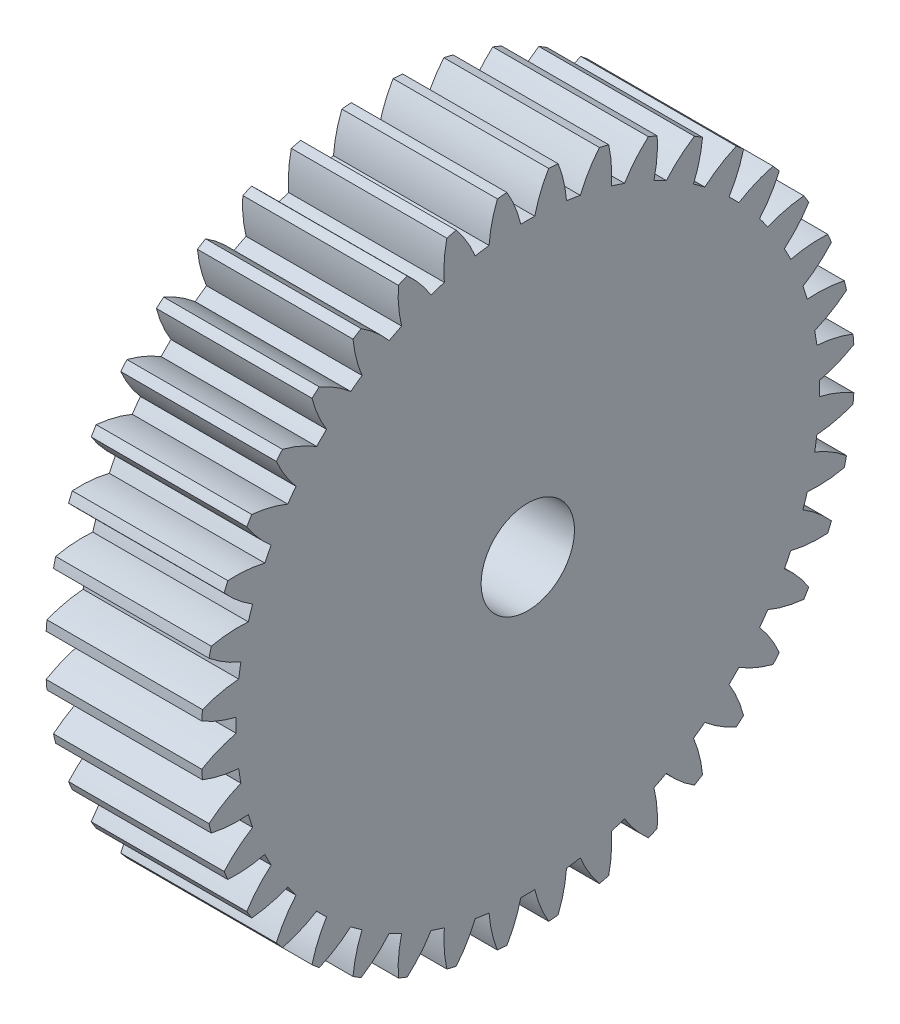
SolidWorks part; units mm, degrees
material "1.0035 (S185)"
ref_plane "Plane1" through (0, 0, 0) normal (0, 0, 1) x (1, 0, 0)
ref_plane "Plane2" through (0, 0, 0) normal (0, 1, 0) x (1, 0, 0)
ref_plane "Plane3" through (0, 0, 0) normal (1, 0, 0) x (0, 0, -1)
sketch "HoldingSke" plane through (0, 0, 0) normal (0, 1, 0) x (1, 0, 0)
  line L0 (0, 0) -> (1.5321, -1.2856)
  line L1 (-15, 0) -> (100, 0) construction
  line L2 (0, 0) -> (-2.1039, 2.3779)
  line L3 (0, 0) -> (-11.863, 4.5341)
  line L4 (0, 0) -> (6.6156, 5.5511)
  line L5 (0, 0) -> (-46.8476, -17.4728)
  line L6 (0, 0) -> (-4.1448, -2.7965)
  line L7 (-2.1039, 2.3779) -> (8.6586, 51.2059)
  line L8 (-76.2, 54.61) -> (-75.7, 54.61)
  line L9 (-71.009, 38.7566) -> (-53.1078, 45.2721)
  line L10 (-76.2, 71.12) -> (104.1128, 71.12)
  line L11 (0, 0) -> (-5, 0)
  line L12 (-76.2, 101.6) -> (-76.181, 101.6)
  line L13 (24.9733, 27.94) -> (52.9518, 28.4284)
  line L14 (24.9733, 27.94) -> (24.9743, 27.94)
  line L15 (24.9733, 27.94) -> (100.4006, 29.5858)
  line L16 (-63.627, -0.5) -> (-12.827, -0.5)
  circle A0 centre (0, 0) radius 1.5
  circle A1 centre (0, 0) radius 9.374
  circle A2 centre (0, 0) radius 37.5
  circle A3 centre (0, 0) radius 1.5
  dimension "MHD" = 18.748
  dimension "Hub_dia" = 75
  dimension "Bore" = 3
  dimension "MBD" = 3
  dimension "Num_teeth" = 40
  dimension "Pitch_radius" = 180.3128
  dimension "Pitch" = 2
  dimension "Width" = 5
  dimension "Overall_len" = 50
  dimension "Show_teeth" = 40
  dimension "Thickness" = 5
  dimension "OAL" = 50.0001
  dimension "T_dim" = 0.5
  dimension "Ap" = 20
  dimension "H" = 19.05
  dimension "Backlash" = 0.019
  dimension "Addendum_fac" = 1
  dimension "Dedendum_fac" = 1.25
  dimension "Clearance_fac" = 0.25
  dimension "Dedendum_add" = 0.001
  dimension "Module" = 0.5
sketch "BasProSke" plane through (0, 0, 0) normal (0, 1, 0) x (1, 0, 0)
  line L0 (-10, 0) -> (60, 0) construction
  line L1 (0, 0) -> (0, 10.5)
  line L2 (0, 0) -> (5, 0)
  line L3 (5, 0) -> (5, 10.5)
  line L4 (5, 10.5) -> (0, 10.5)
  dimension "Diameter" = 21
  dimension "Thickness" = 5
revolve "Base-Revolve" add sketch "BasProSke" angle 360 about L0
sketch "TooCutSke" plane through (0, 0, 0) normal (1, 0, 0) x (0, 0, -1)
  line L1 (0, 0) -> (0, 107) construction
  line L2 (0, 0) -> (-0.4258, 9.9909) construction
  line L3 (0, 0) -> (-1.5682, 19.9255) construction
  line L4 (-0.4258, 9.9909) -> (-0.7841, 9.9627) construction
  arc A0 (0.2242, 9.3713) -> (-0.2242, 9.3713) centre (0, 0) ccw
  arc A1 (0.6847, 10.5031) -> (-0.6847, 10.5031) centre (0, 0) ccw
  circle A2 centre (0, 0) radius 10 construction
  circle A3 centre (0, 0) radius 9.3969 construction
  arc A4 (-0.2242, 9.3713) -> (-0.6847, 10.5031) centre (-4.1161, 8.4475) ccw
  arc A5 (0.6847, 10.5031) -> (0.2242, 9.3713) centre (4.1161, 8.4475) ccw
  dimension "Root_dia" = 18.748
  dimension "Overcut_dia" = 21.0508
  dimension "Pitch_dia" = 20
  dimension "Base_dia" = 18.7939
  dimension "Flank_rad" = 4
  dimension "Half_ang" = 4.5
  dimension "Half_CT" = 0.3593
extrude "ToothCut" cut sketch "TooCutSke" along normal through all
fillet "Breaks" [suppressed] radius 0.01
fillet "RootFillets" [suppressed] radius 0.126
pattern_circular "TeethCuts" count 40 every 9 about axis through (-10, 0, 0) along (1, 0, 0) of "ToothCut", "RootFillets", "Breaks"
sketch "HubNeaOneSke" plane through (0, 0, 0) normal (-1, 0, 0) x (0, 0, 1)
  circle A0 centre (0, 0) radius 9.374
  dimension "Diameter" = 18.748
extrude "HubNearOne" [suppressed] add sketch "HubNeaOneSke" along normal blind 45.0001
sketch "HubNeaBotSke" plane through (0, 0, 0) normal (-1, 0, 0) x (0, 0, 1)
  circle A0 centre (0, 0) radius 9.374
  dimension "Diameter" = 18.748
extrude "HubNearBoth" [suppressed] add sketch "HubNeaBotSke" along normal blind 22.5
ref_plane "FarPln" through (5, 0, 0) normal (1, 0, 0) x (0, 0, -1)
sketch "HubFarSke" plane through (5, 0, 0) normal (1, 0, 0) x (0, 0, -1)
  circle A0 centre (0, 0) radius 9.374
  dimension "Diameter" = 18.748
extrude "HubFar" [suppressed] add sketch "HubFarSke" along normal blind 22.5
sketch "BorSke" plane through (0, 0, 0) normal (1, 0, 0) x (0, 0, -1)
  circle A0 centre (0, 0) radius 1.5
  dimension "Diameter" = 3
extrude "Bore" cut sketch "BorSke" along normal mid plane 100.0001
sketch "KeySke" plane through (0, 0, 0) normal (1, 0, 0) x (0, 0, -1)
  line L0 (-0.6, 0) -> (-0.6, 2)
  line L1 (-0.6, 2) -> (0.6, 2)
  line L2 (0.6, 2) -> (0.6, 0)
  line L3 (0, 0) -> (0, 34) construction
  line L4 (-0.6, 0) -> (0.6, 0)
  dimension "Offset" = 2
  dimension "Width" = 1.2
extrude "Keyway" [suppressed] cut sketch "KeySke" along normal mid plane 100.0001
pattern_circular "Keyway2" [suppressed] count 2 every 90 about axis through (-10, 0, 0) along (1, 0, 0)
equation "' \"Module@HoldingSke\" = 6.35"
equation "' \"Num_teeth@HoldingSke\" = 12"
equation "' \"Ap@HoldingSke\" =  20"
equation "' \"Width@HoldingSke\" = 0.5 * 25.4"
equation "' \"Hub_dia@HoldingSke\"= 1 * 25.4"
equation "' \"Overall_len@HoldingSke\" = 1.0 * 25.4"
equation "' \"Bore@HoldingSke\" = 0.75 * 25.4"
equation "' \"T_dim@HoldingSke\" = 0.1 * 25.4"
equation "' \"Width@KeySke\" = 0.25 * 25.4"
equation "' \"Show_teeth@HoldingSke\" = 13"
equation "' \"Backlash@HoldingSke\" = 0.009 * 25.4"
equation "' \"Addendum_fac@HoldingSke\" = 1.0"
equation "' \"Dedendum_fac@HoldingSke\" = 1.25"
equation "' \"Dedendum_add@HoldingSke\" = 0.00005 * 25.4"
equation "' \"Clearance_fac@HoldingSke\" = 0.25"
equation "\"Pitch@HoldingSke\" = 1 / \"Module@HoldingSke\""
equation "\"Overcut_dia@TooCutSke\" = (\"Num_teeth@HoldingSke\" + 2 * \"Addendum_fac@HoldingSke\") / \"Pitch@HoldingSke\" + 0.002 * 25.4"
equation "\"Pitch_dia@TooCutSke\" = \"Num_teeth@HoldingSke\" / \"Pitch@HoldingSke\""
equation "\"Base_dia@TooCutSke\" = \"Num_teeth@HoldingSke\" / \"Pitch@HoldingSke\" * cos((\"Ap@HoldingSke\"  * 3.14159265 / 180))"
equation "\"Root_dia@TooCutSke\" = (\"Num_teeth@HoldingSke\" + 2) / \"Pitch@HoldingSke\" - 2 * (\"Addendum_fac@HoldingSke\" + \"Dedendum_fac@HoldingSke\") / \"Pitch@HoldingSke\" - \"Dedendum_add@HoldingSke\" * 2"
equation "\"Half_ang@TooCutSke\" = 180 / \"Num_teeth@HoldingSke\""
equation "\"Half_CT@TooCutSke\" = \"Num_teeth@HoldingSke\" / \"Pitch@HoldingSke\" * sin((3.14159265 / 2 / \"Num_teeth@HoldingSke\")) / 2 - 7 * \"Backlash@HoldingSke\" / 4"
equation "\"Flank_rad@TooCutSke\" = \"Num_teeth@HoldingSke\" / \"Pitch@HoldingSke\" / 5"
equation "\"Radius@RootFillets\" = \"Clearance_fac@HoldingSke\" / \"Pitch@HoldingSke\" + \"Dedendum_add@HoldingSke\""
equation "\"Break_rad@Breaks\" = 0.02 / \"Pitch@HoldingSke\""
equation "\"Thickness@HoldingSke\" = \"Width@HoldingSke\""
equation "\"OAL@HoldingSke\" = \"Thickness@HoldingSke\""
equation "\"MHD@HoldingSke\" = (\"Num_teeth@HoldingSke\" + 2) / \"Pitch@HoldingSke\" - 2 * (\"Addendum_fac@HoldingSke\" + \"Dedendum_fac@HoldingSke\")  / \"Pitch@HoldingSke\" - \"Dedendum_add@HoldingSke\" * 2"
equation "\"MBD@HoldingSke\" = (\"Num_teeth@HoldingSke\" + 2) / \"Pitch@HoldingSke\" - 2 * (\"Addendum_fac@HoldingSke\" + \"Dedendum_fac@HoldingSke\")  / \"Pitch@HoldingSke\" - \"Dedendum_add@HoldingSke\" * 2 - 0.002 * 25.4"
equation "\"MHD@HoldingSke\" = ((sgn( \"MHD@HoldingSke\" - \"Hub_dia@HoldingSke\" )-1)*( \"MHD@HoldingSke\" - \"Hub_dia@HoldingSke\" ))/-2+ \"Hub_dia@HoldingSke\""
equation "\"MBD@HoldingSke\" = ((sgn( \"MBD@HoldingSke\" - \"Bore@HoldingSke\" )-1)*( \"MBD@HoldingSke\" - \"Bore@HoldingSke\" ))/-2+ \"Bore@HoldingSke\""
equation "\"OAL@HoldingSke\" = ((sgn( \"OAL@HoldingSke\" - \"Overall_len@HoldingSke\" )+1)*( \"OAL@HoldingSke\" - \"Overall_len@HoldingSke\" ))/2 + \"Overall_len@HoldingSke\" + 0.000002 * 25.4"
equation "\"Num_teeth@TeethCuts\" = int( \"Show_teeth@HoldingSke\" ) + 1"
equation "\"Num_teeth@TeethCuts\" = ((sgn( \"Num_teeth@TeethCuts\" - \"Num_teeth@HoldingSke\" )-1)*( \"Num_teeth@TeethCuts\" - \"Num_teeth@HoldingSke\" ))/-2+ \"Num_teeth@HoldingSke\""
equation "\"Num_teeth@TeethCuts\" = ((sgn( \"Num_teeth@TeethCuts\" - 2.0)+1)*( \"Num_teeth@TeethCuts\" - 2.0))/2 +2.0"
equation "\"Angle@TeethCuts\" = 360.0 / \"Num_teeth@HoldingSke\""
equation "\"Diameter@BasProSke\" = (\"Num_teeth@HoldingSke\" + 2 * \"Addendum_fac@HoldingSke\") / \"Pitch@HoldingSke\""
equation "\"Thickness@BasProSke\"  = \"Thickness@HoldingSke\""
equation "' \"Fillet_rad@BasProSke\" =  \"Thickness@HoldingSke\" * 0.05"
equation "\"MHD@HoldingSke\" = ((sgn( \"MHD@HoldingSke\" - \"Root_dia@TooCutSke\" )-1)*( \"MHD@HoldingSke\" - \"Root_dia@TooCutSke\" ))/-2+ \"Root_dia@TooCutSke\""
equation "\"Diameter@HubNeaOneSke\" = \"MHD@HoldingSke\""
equation "\"Length@HubNearOne\" = \"OAL@HoldingSke\" - \"Thickness@BasProSke\""
equation "\"Diameter@HubNeaBotSke\" = \"MHD@HoldingSke\""
equation "\"Length@HubNearBoth\" = ( \"OAL@HoldingSke\" - \"Thickness@BasProSke\" ) / 2.0"
equation "\"Thickness@FarPln\" = \"Thickness@BasProSke\""
equation "\"Diameter@HubFarSke\" = \"MHD@HoldingSke\""
equation "\"Length@HubFar\" = ( \"OAL@HoldingSke\" - \"Thickness@BasProSke\" ) / 2.0"
equation "\"Diameter@BorSke\" = \"MBD@HoldingSke\""
equation "\"D1@Bore\" = \"OAL@HoldingSke\" * 2.0"
equation "\"D1@Keyway\" = \"OAL@HoldingSke\" * 2.0"
equation "\"Offset@KeySke\" = \"T_dim@HoldingSke\" + \"MBD@HoldingSke\" / 2.0"
